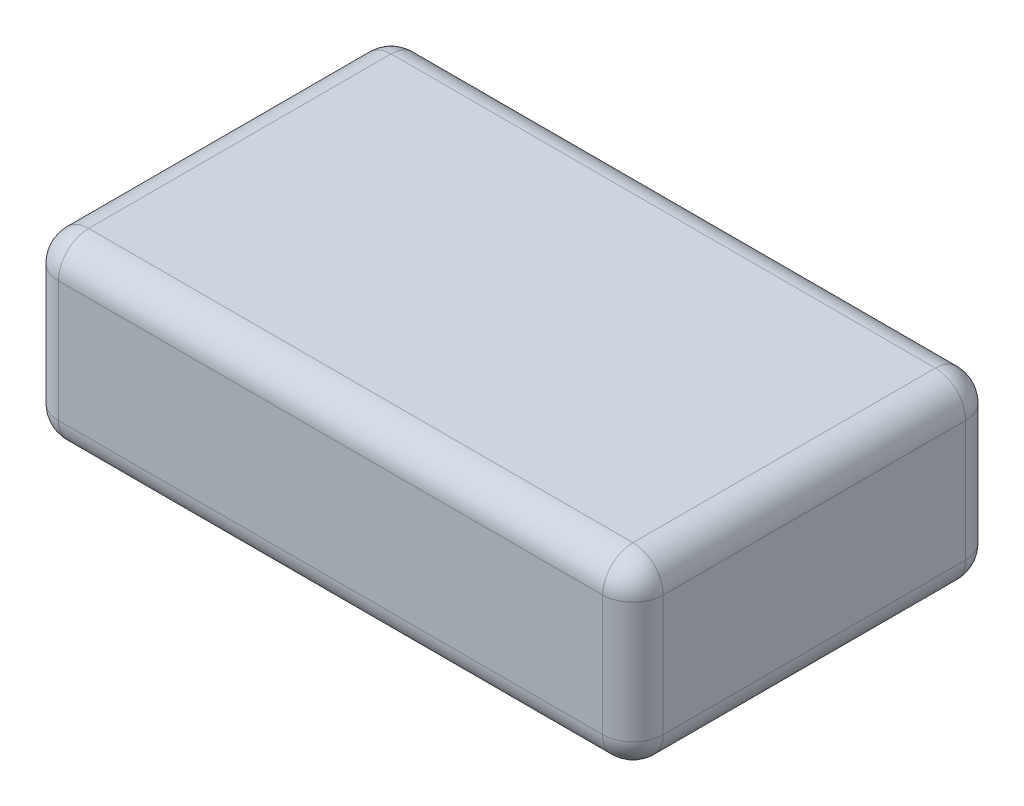
SolidWorks part; units mm, degrees
ref_plane "Front Plane" through (0, 0, 0) normal (0, 0, 1) x (1, 0, 0)
ref_plane "Top Plane" through (0, 0, 0) normal (0, 1, 0) x (1, 0, 0)
ref_plane "Right Plane" through (0, 0, 0) normal (1, 0, 0) x (0, 0, -1)
other "Bounding Box"
ref_plane "Default Plane" through (-8.9266, -12.7485, 0) normal (-0.1736, 0.9848, 0) x (0.9848, 0.1736, 0)
sketch "Sketch1" plane through (0, 0, 0) normal (0, 1, 0) x (1, 0, 0)
  line L1 (-31.75, 19.05) -> (31.75, 19.05)
  line L2 (-31.75, 19.05) -> (-31.75, -19.05)
  line L3 (-31.75, -19.05) -> (31.75, -19.05)
  line L4 (31.75, 19.05) -> (31.75, -19.05)
  line L5 (-31.75, 19.05) -> (31.75, -19.05) construction
  line L6 (-31.75, -19.05) -> (31.75, 19.05) construction
  point P0 (0, 0)
  dimension "D1" = 63.5
  dimension "D2" = 38.1
extrude "Boss-Extrude1" add sketch "Sketch1" along normal blind 19.05
fillet "Fillet1" radius 3.175 12 edges at (-31.75, 19.05, 0) (0, 19.05, -19.05) (-31.75, 9.525, -19.05) (31.75, 19.05, 0) (31.75, 9.525, -19.05) (-31.75, 9.525, 19.05) (0, 19.05, 19.05) (31.75, 9.525, 19.05) (0, 0, -19.05) (-31.75, 0, 0) (0, 0, 19.05) (31.75, 0, 0)
